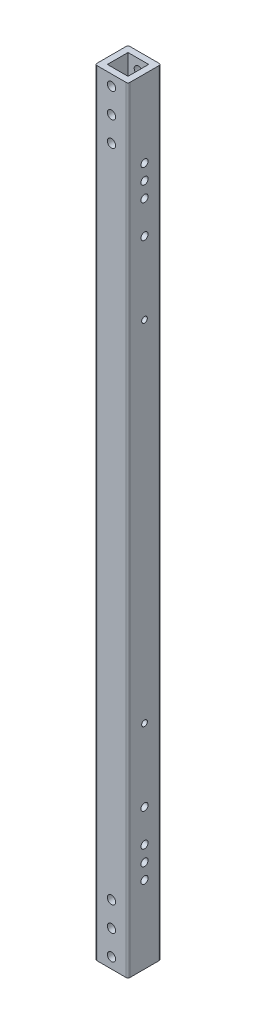
SolidWorks part; units mm, degrees
material "1060 Alloy"
ref_plane "Front Plane" through (0, 0, 0) normal (0, 0, 1) x (1, 0, 0)
ref_plane "Top Plane" through (0, 0, 0) normal (0, 1, 0) x (1, 0, 0)
ref_plane "Right Plane" through (0, 0, 0) normal (1, 0, 0) x (0, 0, -1)
sketch "Sketch1" plane through (0, 0, 0) normal (0, 1, 0) x (1, 0, 0)
  line L0 (-7.9375, 7.9375) -> (7.9375, 7.9375)
  line L1 (-12.7, -12.7) -> (12.7, -12.7)
  line L2 (-12.7, -12.7) -> (-12.7, 12.7)
  line L3 (-12.7, 12.7) -> (12.7, 12.7)
  line L4 (12.7, -12.7) -> (12.7, 12.7)
  line L5 (-12.7, -12.7) -> (12.7, 12.7) construction
  line L6 (-12.7, 12.7) -> (12.7, -12.7) construction
  line L7 (7.9375, -7.9375) -> (7.9375, 7.9375)
  line L8 (-7.9375, -7.9375) -> (7.9375, -7.9375)
  line L9 (-7.9375, -7.9375) -> (-7.9375, 7.9375)
  point P0 (0, 0)
  dimension "D1" = 25.4
  dimension "D2" = 4.7625
extrude "Boss-Extrude1" add sketch "Sketch1" along normal mid plane 596
fillet "Fillet1" radius 1.5 4 edges at (-12.7, 0, -12.7) (12.7, 0, -12.7) (-12.7, 0, 12.7) (12.7, 0, 12.7)
hole_wizard "1/4 (0.25) Diameter Hole1" positions "3DSketch3" profile "Sketch3" hole size "1/4" standard "ANSI Inch" end condition through all
sketch3d "3DSketch3"
  line L0 (0.0118, 289.825, -12.7) -> (0.0118, 251.825, -12.7) construction
  line L2 (11.2, 298, -12.7) -> (-11.2, 298, -12.7) construction
  line L3 (-12.7, 298, -11.2) -> (-12.7, -298, -11.2) construction
  point P0 (0.0118, 289.825, -12.7)
  point P2 (0.0118, 270.825, -12.7)
  point P4 (0.0118, 251.825, -12.7)
  point P16 (0.0118, 270.825, -12.7)
  dimension "D1" = 38
  dimension "D2" = 8.175
  dimension "D3" = 12.8
sketch "Sketch3" plane through (0.0118, 289.825, -12.7) normal (1, 0, 0) x (0, 1, 0)
  line L0 (0, 0) -> (0, 25.4)
  line L1 (0, 25.4) -> (3.175, 25.4)
  line L2 (3.175, 25.4) -> (3.175, 0)
  line L5 (3.175, 0) -> (0, 0)
  line L11 (0, -6.35) -> (0, 107.95) construction
  dimension "Thru Hole Dia." = 6.35
  dimension "Thru Hole Depth" = 25.4
mirror "Mirror1" about plane through (0, 0, 0) normal (0, 1, 0) of "1/4 (0.25) Diameter Hole1"
sketch "Sketch4" plane through (-12.7, 0, 0) normal (-1, 0, 0) x (0, 0, 1)
  line L0 (-11.2, 298) -> (11.2, 298) construction
  line L1 (-1000, 0) -> (49000, 0) construction
  line L3 (-22.8667, 248.65) -> (51.7546, 248.65) construction
  circle A1 centre (0, 134.3) radius 2.2
  circle A2 centre (0, -134.3) radius 2.2
  circle A3 centre (0, 238.65) radius 2.75
  circle A4 centre (0, 226.9) radius 2.75
  circle A5 centre (0, 215.15) radius 2.75
  circle A6 centre (0, -215.15) radius 2.75
  circle A7 centre (0, -226.9) radius 2.75
  circle A8 centre (0, -238.65) radius 2.75
  circle A9 centre (0, 190) radius 2.75
  circle A10 centre (0, -190) radius 2.75
  point P0 (0, 134.3)
  point P6 (0, 298)
  point P28 (0, 0)
  dimension "D2" = 4.4
  dimension "D3" = 5.5
  dimension "D4" = 11.75
  dimension "D5" = 11.75
  dimension "D6" = 10
  dimension "D7" = 108
  dimension "D1" = 163.7
extrude "Cut-Extrude1" cut sketch "Sketch4" against normal through all
